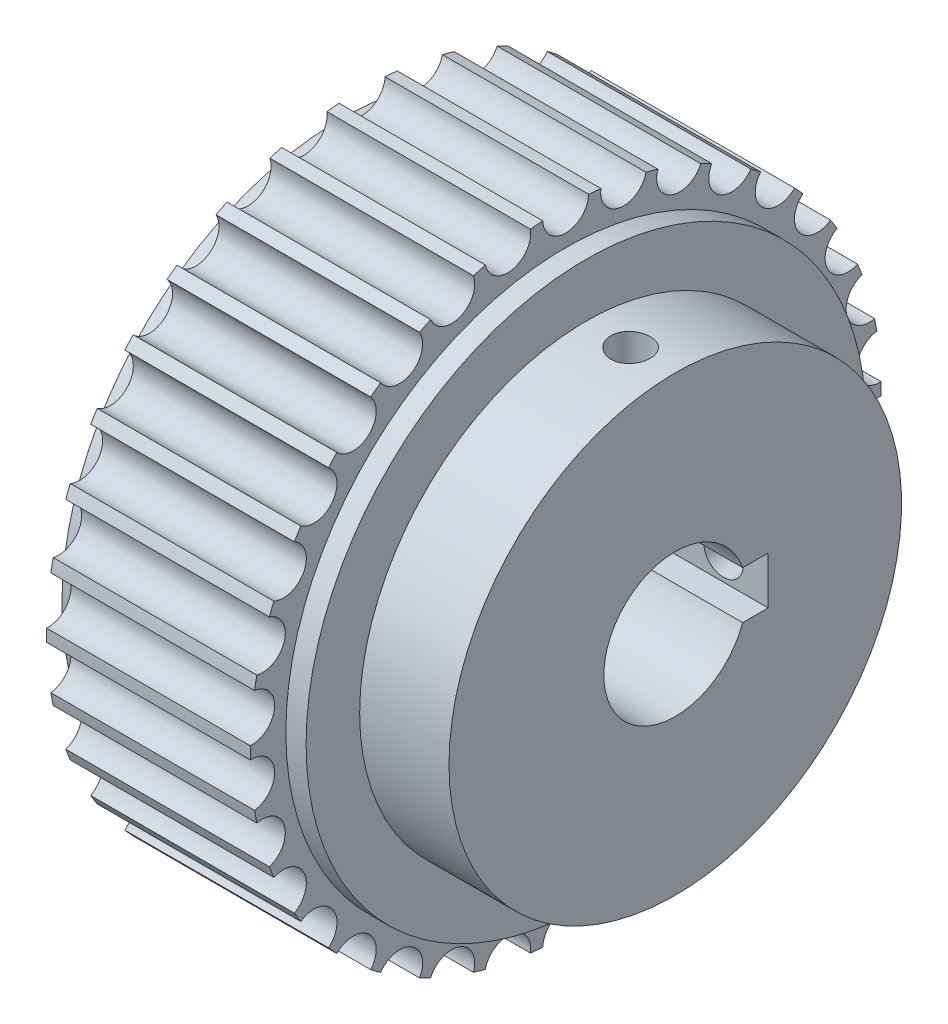
SolidWorks part; units mm, degrees
ref_plane "Front" through (0, 0, 0) normal (0, 0, 1) x (1, 0, 0)
ref_plane "Top" through (0, 0, 0) normal (0, 1, 0) x (1, 0, 0)
ref_plane "Right" through (0, 0, 0) normal (1, 0, 0) x (0, 0, -1)
sketch "Sketch1" plane through (0, 0, 0) normal (0, 0, 1) x (1, 0, 0)
  line L0 (0, 0) -> (64.6735, 0) construction
  line L1 (-10.25, 6) -> (17.75, 6)
  line L2 (17.75, 6) -> (17.75, 19)
  line L3 (-10.25, 23.5) -> (-8.55, 23.5)
  line L4 (8.55, 23.5) -> (10.25, 23.5)
  line L5 (10.25, 23.5) -> (10.25, 19)
  line L6 (8.55, 23.5) -> (8.55, 26.485)
  line L7 (8.55, 26.485) -> (-8.55, 26.485)
  line L8 (-8.55, 26.485) -> (-8.55, 23.5)
  line L9 (10.25, 19) -> (17.75, 19)
  line L12 (-10.25, 23.5) -> (-10.25, 6)
  point P4 (0, 26.485)
  dimension "D1" = 7.5
  dimension "D2" = 20.5
  dimension "D3" = 1.7
  dimension "D4" = 47
  dimension "D5" = 52.97
  dimension "D6" = 38
  dimension "D7" = 12
revolve "Revolve1" add sketch "Sketch1" angle 360 about L0
sketch "Sketch2" plane through (-8.55, 0, 0) normal (-1, 0, 0) x (0, 0, 1)
  circle A0 centre (0, 26.485) radius 1.93
  circle A1 centre (0, 0) radius 26.485 construction
  dimension "D1" = 3.86
extrude "Cut-Extrude1" cut sketch "Sketch2" against normal through all
pattern_circular "CirPattern1" count 34 over 360 about axis through (0, 0, 0) along (1, 0, 0) of "Cut-Extrude1"
hole_wizard "M4x0.7 Tapped Hole1" positions "Sketch7" profile "Sketch6" tap size "M4x0.7" standard "ANSI Metric"
sketch "Sketch7" plane through (0, 0, 0) normal (0, 1, 0) x (1, 0, 0)
  line L0 (17.75, 0) -> (-10.25, 0) construction
  line L1 (10.25, 0) -> (17.75, 0) construction
  line L2 (10.25, -19) -> (10.25, 19) construction
  line L4 (17.75, -19) -> (17.75, 19) construction
  point P0 (14, 0)
sketch "Sketch6" plane through (14, 0, 0) normal (1, 0, 0) x (0, 0, -1)
  line L0 (0, 0) -> (0, 19.001)
  line L1 (0, 19.001) -> (1.65, 19.001)
  line L2 (1.65, 19.001) -> (1.65, 0)
  line L5 (1.65, 0) -> (0, 0)
  line L11 (0, -6.35) -> (0, 107.95) construction
  dimension "Thru Tap Drill Dia." = 3.3
  dimension "Thru Tap Drill Depth" = 19.001
cosmetic thread "Hole Thread1" parameters "D2"=4
pattern_circular "CirPattern2" count 2 over 90 about axis through (0, 0, 0) along (-1, 0, 0) of "M4x0.7 Tapped Hole1"
sketch "Sketch8" plane through (17.75, 0, 0) normal (1, 0, 0) x (0, 0, -1)
  line L0 (18.9282, 0) -> (5.7687, 0) construction
  line L1 (4.2, 2) -> (7.8, 2)
  line L2 (4.2, 2) -> (4.2, -2)
  line L3 (4.2, -2) -> (7.8, -2)
  line L4 (7.8, 2) -> (7.8, -2)
  line L5 (6, -2) -> (6, 2) construction
  line L6 (4.2, 0) -> (7.8, 0) construction
  line L7 (7.8, 0) -> (-6, 0) construction
  circle A0 centre (0, 0) radius 6 construction
  point P0 (6, 0)
  dimension "D1" = 4
  dimension "D2" = 13.8
extrude "Cut-Extrude2" cut sketch "Sketch8" against normal through all
sketch "Sketch9" plane through (-10.25, 0, 0) normal (-1, 0, 0) x (0, 0, 1)
  circle A0 centre (0, 0) radius 16.5
  dimension "D1" = 33
extrude "Cut-Extrude3" cut sketch "Sketch9" against normal blind 5.7
